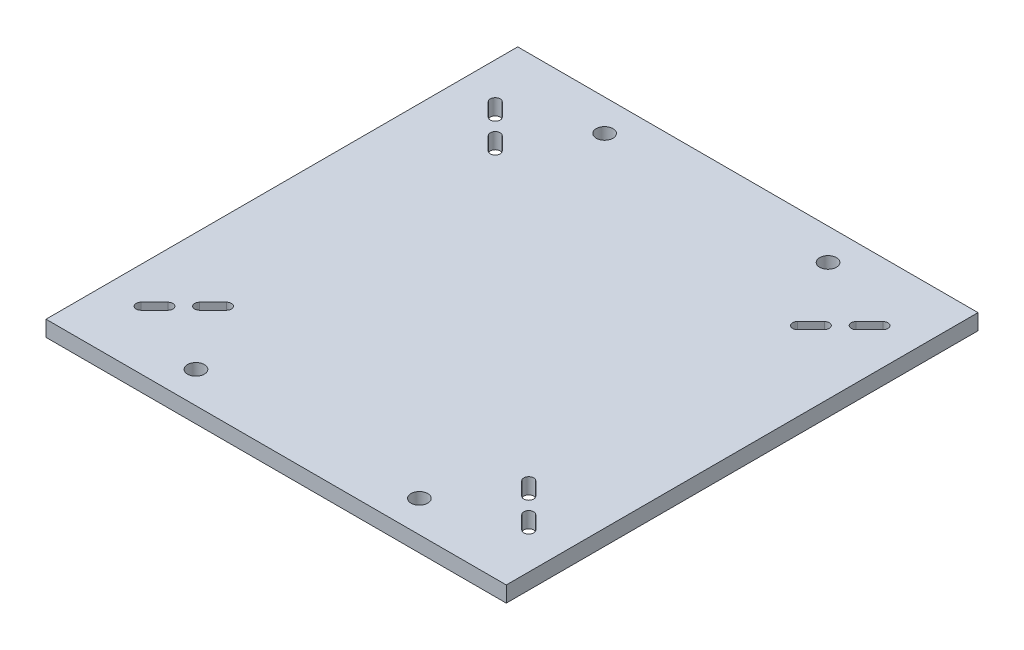
SolidWorks part; units mm, degrees
material "6061-T6 (SS)"
ref_plane "Front Plane" through (0, 0, 0) normal (0, 0, 1) x (1, 0, 0)
ref_plane "Top Plane" through (0, 0, 0) normal (0, 1, 0) x (1, 0, 0)
ref_plane "Right Plane" through (0, 0, 0) normal (1, 0, 0) x (0, 0, -1)
sketch "Sketch1" plane through (0, 0, 0) normal (0, 1, 0) x (1, 0, 0)
  line L1 (0, 0) -> (185.4, 0)
  line L2 (0, 0) -> (0, -190)
  line L3 (0, -190) -> (185.4, -190)
  line L4 (185.4, 0) -> (185.4, -190)
  dimension "D1" = 185.4
  dimension "D2" = 190
extrude "base plate" add sketch "Sketch1" against normal blind 6.35
sketch "center lines" plane through (0, 0, 0) normal (0, 1, 0) x (1, 0, 0)
  line L0 (92.7, 0) -> (92.7, -190) construction
  line L1 (185.4, 0) -> (0, 0) construction
  line L2 (0, -190) -> (185.4, -190) construction
  line L3 (0, -95) -> (185.4, -95) construction
  line L4 (0, 0) -> (0, -190) construction
  line L5 (185.4, -190) -> (185.4, 0) construction
sketch "Sketch3" plane through (0, 0, 0) normal (0, 1, 0) x (1, 0, 0)
  line L0 (1.825, -168.3487) -> (12.6013, -179.125)
  line L1 (12.6013, -179.125) -> (46.7263, -145)
  line L2 (46.7263, -145) -> (35.95, -134.2237)
  line L3 (35.95, -134.2237) -> (1.825, -168.3487)
  line L4 (14.6222, -166.3278) -> (20.0104, -160.9396) construction
  line L5 (13.208, -164.9135) -> (18.5962, -159.5254)
  line L6 (16.0365, -167.742) -> (21.4246, -162.3538)
  line L7 (0, -190) -> (185.4, -190) construction
  line L8 (31.8191, -149.1309) -> (26.4309, -154.5191) construction
  line L9 (33.2333, -150.5451) -> (27.8451, -155.9333)
  line L10 (92.7, 0) -> (92.7, -190) construction
  line L11 (0, -95) -> (185.4, -95) construction
  line L12 (46.7263, -45) -> (35.95, -55.7763)
  line L13 (12.6013, -10.875) -> (46.7263, -45)
  line L14 (1.825, -21.6513) -> (12.6013, -10.875)
  line L15 (35.95, -55.7763) -> (1.825, -21.6513)
  line L16 (172.7987, -10.875) -> (138.6737, -45)
  line L17 (183.575, -21.6513) -> (172.7987, -10.875)
  line L18 (149.45, -55.7763) -> (183.575, -21.6513)
  line L19 (138.6737, -45) -> (149.45, -55.7763)
  line L20 (138.6737, -145) -> (149.45, -134.2237)
  line L21 (172.7987, -179.125) -> (138.6737, -145)
  line L22 (183.575, -168.3487) -> (172.7987, -179.125)
  line L23 (149.45, -134.2237) -> (183.575, -168.3487)
  line L24 (30.4049, -147.7167) -> (25.0167, -153.1049)
  line L25 (14.6222, -23.6722) -> (20.0104, -29.0604) construction
  line L26 (13.208, -25.0865) -> (18.5962, -30.4746)
  line L27 (16.0365, -22.258) -> (21.4246, -27.6462)
  line L28 (31.8191, -40.8691) -> (26.4309, -35.4809) construction
  line L29 (33.2333, -39.4549) -> (27.8451, -34.0667)
  line L30 (30.4049, -42.2833) -> (25.0167, -36.8951)
  line L31 (170.7778, -23.6722) -> (165.3896, -29.0604) construction
  line L32 (172.192, -25.0865) -> (166.8038, -30.4746)
  line L33 (169.3635, -22.258) -> (163.9754, -27.6462)
  line L34 (153.5809, -40.8691) -> (158.9691, -35.4809) construction
  line L35 (152.1667, -39.4549) -> (157.5549, -34.0667)
  line L36 (154.9951, -42.2833) -> (160.3833, -36.8951)
  line L37 (153.5809, -149.1309) -> (158.9691, -154.5191) construction
  line L38 (152.1667, -150.5451) -> (157.5549, -155.9333)
  line L39 (154.9951, -147.7167) -> (160.3833, -153.1049)
  line L40 (170.7778, -166.3278) -> (165.3896, -160.9396) construction
  line L41 (172.192, -164.9135) -> (166.8038, -159.5254)
  line L42 (169.3635, -167.742) -> (163.9754, -162.3538)
  line L43 (35.95, -145) -> (35.95, -134.2237)
  line L44 (46.7263, -145) -> (35.95, -145)
  line L45 (35.95, -45) -> (35.95, -55.7763)
  line L46 (46.7263, -45) -> (35.95, -45)
  line L47 (149.45, -45) -> (149.45, -55.7763)
  line L48 (138.6737, -45) -> (149.45, -45)
  line L49 (149.45, -145) -> (149.45, -134.2237)
  line L50 (138.6737, -145) -> (149.45, -145)
  line L53 (185.4, 0) -> (0, 0) construction
  arc A0 (13.208, -164.9135) -> (16.0365, -167.742) centre (14.6222, -166.3278) ccw
  arc A1 (21.4246, -162.3538) -> (18.5962, -159.5254) centre (20.0104, -160.9396) ccw
  arc A2 (33.2333, -150.5451) -> (30.4049, -147.7167) centre (31.8191, -149.1309) ccw
  arc A3 (25.0167, -153.1049) -> (27.8451, -155.9333) centre (26.4309, -154.5191) ccw
  arc A4 (13.208, -25.0865) -> (16.0365, -22.258) centre (14.6222, -23.6722) cw
  arc A5 (21.4246, -27.6462) -> (18.5962, -30.4746) centre (20.0104, -29.0604) cw
  arc A6 (33.2333, -39.4549) -> (30.4049, -42.2833) centre (31.8191, -40.8691) cw
  arc A7 (25.0167, -36.8951) -> (27.8451, -34.0667) centre (26.4309, -35.4809) cw
  arc A8 (172.192, -25.0865) -> (169.3635, -22.258) centre (170.7778, -23.6722) ccw
  arc A9 (163.9754, -27.6462) -> (166.8038, -30.4746) centre (165.3896, -29.0604) ccw
  arc A10 (152.1667, -39.4549) -> (154.9951, -42.2833) centre (153.5809, -40.8691) ccw
  arc A11 (160.3833, -36.8951) -> (157.5549, -34.0667) centre (158.9691, -35.4809) ccw
  arc A12 (152.1667, -150.5451) -> (154.9951, -147.7167) centre (153.5809, -149.1309) cw
  arc A13 (160.3833, -153.1049) -> (157.5549, -155.9333) centre (158.9691, -154.5191) cw
  arc A14 (172.192, -164.9135) -> (169.3635, -167.742) centre (170.7778, -166.3278) cw
  arc A15 (163.9754, -162.3538) -> (166.8038, -159.5254) centre (165.3896, -160.9396) cw
  point P29 (17.3163, -163.6337)
  point P36 (29.125, -151.825)
  point P44 (17.3163, -26.3663)
  point P51 (29.125, -38.175)
  point P58 (168.0837, -26.3663)
  point P65 (156.275, -38.175)
  point P72 (156.275, -151.825)
  point P79 (168.0837, -163.6337)
  point P84 (21.4246, -159.5254)
  point P85 (25.0167, -155.9333)
  dimension "D6" = 2
  dimension "D10" = 5.08
  dimension "D9" = 5.842
  dimension "D1" = 48.26
  dimension "D2" = 15.24
  dimension "D3" = 45
  dimension "D4" = 100
  dimension "D5" = 113.5
  dimension "D7" = 7.62
  dimension "D8" = 7.62
extrude "slots" cut sketch "Sketch3" against normal through all contours A5 L27 A4 L26 | L33 A9 L32 A8 | L36 A11 L35 A10 | A13 L39 A12 L38 | A15 L42 A14 L41 | L6 A1 L5 A0 | L24 A3 L9 A2 | L30 A7 L29 A6
hole_wizard "Feet connection hole" positions "Sketch6" profile "Sketch7" hole size "1/4" standard "ANSI Inch" end condition through all
sketch "Sketch6" plane through (0, 0, 0) normal (0, 1, 0) x (1, 0, 0)
  line L0 (0, -190) -> (185.4, -190) construction
  line L3 (185.4, 0) -> (0, 0) construction
  line L4 (92.7, 0) -> (92.7, -190) construction
  point P3 (47.7, -177.3)
  point P19 (137.7, -12.7)
  point P33 (47.7, -12.7)
  point P37 (137.7, -177.3)
  dimension "D1" = 12.7
  dimension "D2" = 90
  dimension "D3" = 45
  dimension "D4" = 12.7
sketch "Sketch7" plane through (47.7, 0, 177.3) normal (1, 0, 0) x (0, 0, 1)
  line L0 (0, 0) -> (0, 6.35)
  line L1 (0, 6.35) -> (3.3782, 6.35)
  line L2 (3.3782, 6.35) -> (3.3782, 0)
  line L5 (3.3782, 0) -> (0, 0)
  line L11 (0, -6.35) -> (0, 107.95) construction
  dimension "Thru Hole Dia." = 6.7564
  dimension "Thru Hole Depth" = 6.35
ref_plane "Center Plane" through (0, 0, 95) normal (0, 0, 1) x (1, 0, 0)
